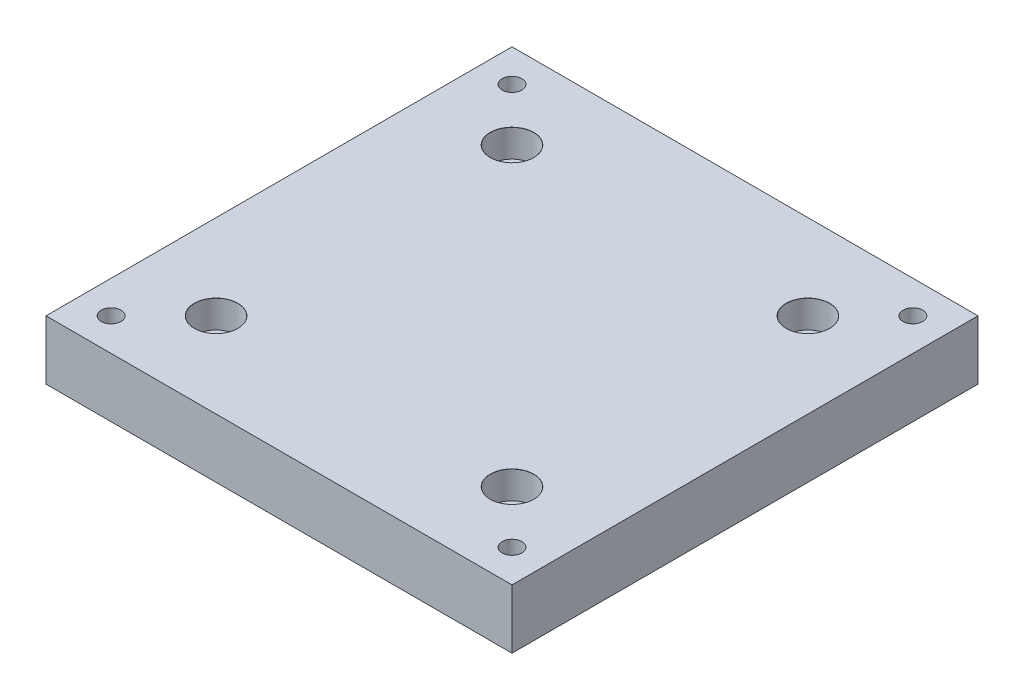
SolidWorks part; units mm, degrees
material "Plain Carbon Steel"
ref_plane "Front Plane" through (0, 0, 0) normal (0, 0, 1) x (1, 0, 0)
ref_plane "Top Plane" through (0, 0, 0) normal (0, 1, 0) x (1, 0, 0)
ref_plane "Right Plane" through (0, 0, 0) normal (1, 0, 0) x (0, 0, -1)
sketch "Sketch1" plane through (0, 0, 0) normal (0, 1, 0) x (1, 0, 0)
  line L1 (-59.055, -59.055) -> (59.055, -59.055)
  line L2 (-59.055, -59.055) -> (-59.055, 59.055)
  line L3 (-59.055, 59.055) -> (59.055, 59.055)
  line L4 (59.055, -59.055) -> (59.055, 59.055)
  line L5 (-59.055, -59.055) -> (59.055, 59.055) construction
  line L6 (-59.055, 59.055) -> (59.055, -59.055) construction
  dimension "D3" = 118.11
  dimension "D4" = 118.11
extrude "Boss-Extrude1" add sketch "Sketch1" against normal blind 15
sketch "Sketch3" plane through (0, 0, 0) normal (0, -1, 0) x (1, 0, 0)
  line L1 (-37.5, -37.5) -> (37.5, -37.5)
  line L2 (-37.5, -37.5) -> (-37.5, 37.5)
  line L3 (-37.5, 37.5) -> (37.5, 37.5)
  line L4 (37.5, -37.5) -> (37.5, 37.5)
  line L5 (-37.5, -37.5) -> (37.5, 37.5) construction
  line L6 (-37.5, 37.5) -> (37.5, -37.5) construction
  line L7 (-50.8, 50.8) -> (50.8, 50.8)
  line L8 (-50.8, 50.8) -> (-50.8, -50.8)
  line L9 (-50.8, -50.8) -> (50.8, -50.8)
  line L10 (50.8, 50.8) -> (50.8, -50.8)
  line L11 (-50.8, 50.8) -> (50.8, -50.8) construction
  line L12 (-50.8, -50.8) -> (50.8, 50.8) construction
  point P0 (0, 0)
  point P6 (0, 0)
  point P7 (-37.5, 37.5)
  point P8 (37.5, 37.5)
  point P9 (37.5, -37.5)
  point P10 (-37.5, -37.5)
  dimension "D1" = 75
  dimension "D2" = 75
  dimension "D3" = 101.6
  dimension "D4" = 101.6
hole_wizard "CBORE for M6 SHCS1" positions "Sketch4" profile "Sketch5" counterbore size "M6" standard "ANSI Metric"
sketch "Sketch4" plane through (0, 0, 0) normal (0, -1, 0) x (-1, 0, 0)
  point P0 (37.5, -37.5)
  point P3 (-37.5, -37.5)
  point P6 (-37.5, 37.5)
  point P9 (37.5, 37.5)
sketch "Sketch5" plane through (-37.5, 0, 37.5) normal (1, 0, 0) x (0, 0, 1)
  line L0 (0, 0) -> (0, 16.9828)
  line L1 (0, 16.9828) -> (3.3, 15)
  line L2 (3.3, 15) -> (3.3, 7)
  line L3 (3.3, 7) -> (5.5, 7)
  line L5 (5.5, 7) -> (5.5, 0.025)
  line L6 (5.5, 0.025) -> (5.525, 0)
  line L7 (5.525, 0) -> (0, 0)
  line L8 (-5.5, 0.025) -> (-5.525, 0) construction
  line L10 (0, 16.9828) -> (-3.3, 15) construction
  line L11 (0, -6.35) -> (0, 107.95) construction
  dimension "Hole Dia." = 6.6
  dimension "Hole Depth" = 15
  dimension "C'Bore Dia." = 11
  dimension "C'Bore Depth" = 7
  dimension "Near C'Sink Dia." = 11.05
  dimension "Near C'Sink Angle" = 90
  dimension "Drill Angle" = 118
hole_wizard "M6x1.0 Tapped Hole1" positions "Sketch6" profile "Sketch7" tap size "M6x1.0" standard "ANSI Metric"
sketch "Sketch6" plane through (0, 0, 0) normal (0, 1, 0) x (1, 0, 0)
  point P0 (-50.8, -50.8)
  point P3 (-50.8, 50.8)
  point P6 (50.8, 50.8)
  point P9 (50.8, -50.8)
sketch "Sketch7" plane through (-50.8, 0, 50.8) normal (1, 0, 0) x (0, 0, 1)
  line L0 (0, 0) -> (0, 11.5022)
  line L1 (0, 11.5022) -> (2.5, 10)
  line L2 (2.5, 10) -> (2.5, 0)
  line L5 (2.5, 0) -> (0, 0)
  line L10 (0, 11.5022) -> (-2.5, 10) construction
  line L11 (0, -6.35) -> (0, 107.95) construction
  dimension "Tap Drill Dia." = 5
  dimension "Tap Drill Depth" = 10
  dimension "Drill Angle" = 118
cosmetic thread "Hole Thread1" parameters "D1"=6.5786, "D2"=6
cosmetic thread "Hole Thread2" parameters "D1"=6.5786, "D2"=6
cosmetic thread "Hole Thread3" parameters "D1"=6.5786, "D2"=6
cosmetic thread "Hole Thread4" parameters "D1"=6.5786, "D2"=6
